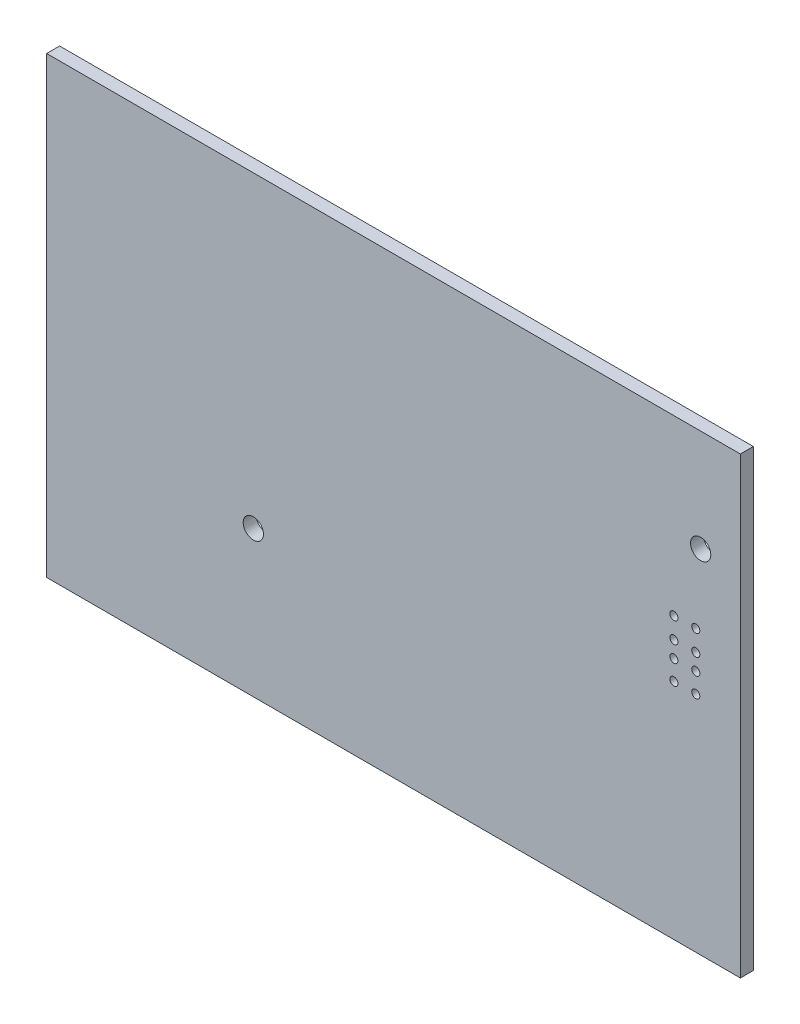
SolidWorks part; units mm, degrees
ref_plane "Plano frontal" through (0, 0, 0) normal (0, 0, 1) x (1, 0, 0)
ref_plane "Plano superior" through (0, 0, 0) normal (0, 1, 0) x (1, 0, 0)
ref_plane "Plano direito" through (0, 0, 0) normal (1, 0, 0) x (0, 0, -1)
ref_plane "Plano1" through (0, 0, 0) normal (0, 0, -1) x (-1, 0, 0)
sketch "Esboço1" plane through (0, 0, 0) normal (0, 0, -1) x (-1, 0, 0)
  line L0 (-42.5, 28) -> (-42.5, -28)
  line L1 (-42.5, -28) -> (43.1, -28)
  line L2 (43.1, -28) -> (43.1, 28)
  line L3 (43.1, 28) -> (-42.5, 28)
  dimension "D1" = 85.6
  dimension "D2" = 56
extrude "Ressalto-extrusão1" add sketch "Esboço1" against normal blind 1.6
sketch "Esboço2" plane through (0, 0, 1.6) normal (0, 0, 1) x (1, 0, 0)
  line L0 (42.5, 28) -> (42.5, -28) construction
  circle A4 centre (37, 6.6) radius 0.5
  circle A5 centre (34.3, 6.6) radius 0.5
  circle A6 centre (34.3, 4.05) radius 0.5
  circle A7 centre (34.3, 2.04) radius 0.5
  circle A8 centre (34.3, -0.4) radius 0.5
  circle A9 centre (37, 4.05) radius 0.5
  circle A10 centre (37, 2.04) radius 0.5
  circle A11 centre (37, -0.4) radius 0.5
  point P18 (42.5, 0)
  dimension "D10" = 5.5
  dimension "D12" = 2.7
  dimension "D14" = 2.55
  dimension "D15" = 2.44
  dimension "D16" = 1
  dimension "D11" = 6.6
extrude "Corte-extrusão1" cut sketch "Esboço2" against normal blind 2
sketch "Esboço3" plane through (0, 0, 1.6) normal (0, 0, 1) x (1, 0, 0)
  line L0 (42.5, 28) -> (42.5, -28) construction
  line L1 (-43.1, 28) -> (42.5, 28) construction
  line L2 (-43.1, -28) -> (-43.1, 28) construction
  line L3 (42.5, -28) -> (-43.1, -28) construction
  circle A0 centre (37.6, 15.4) radius 1.25
  circle A1 centre (-17.6, -10) radius 1.25
  dimension "D2" = 12.6
  dimension "D4" = 18
  dimension "D5" = 2.5
  dimension "D6" = 2.5
  dimension "D1" = 4.9
  dimension "D3" = 25.5
extrude "Corte-extrusão2" cut sketch "Esboço3" against normal blind 10
